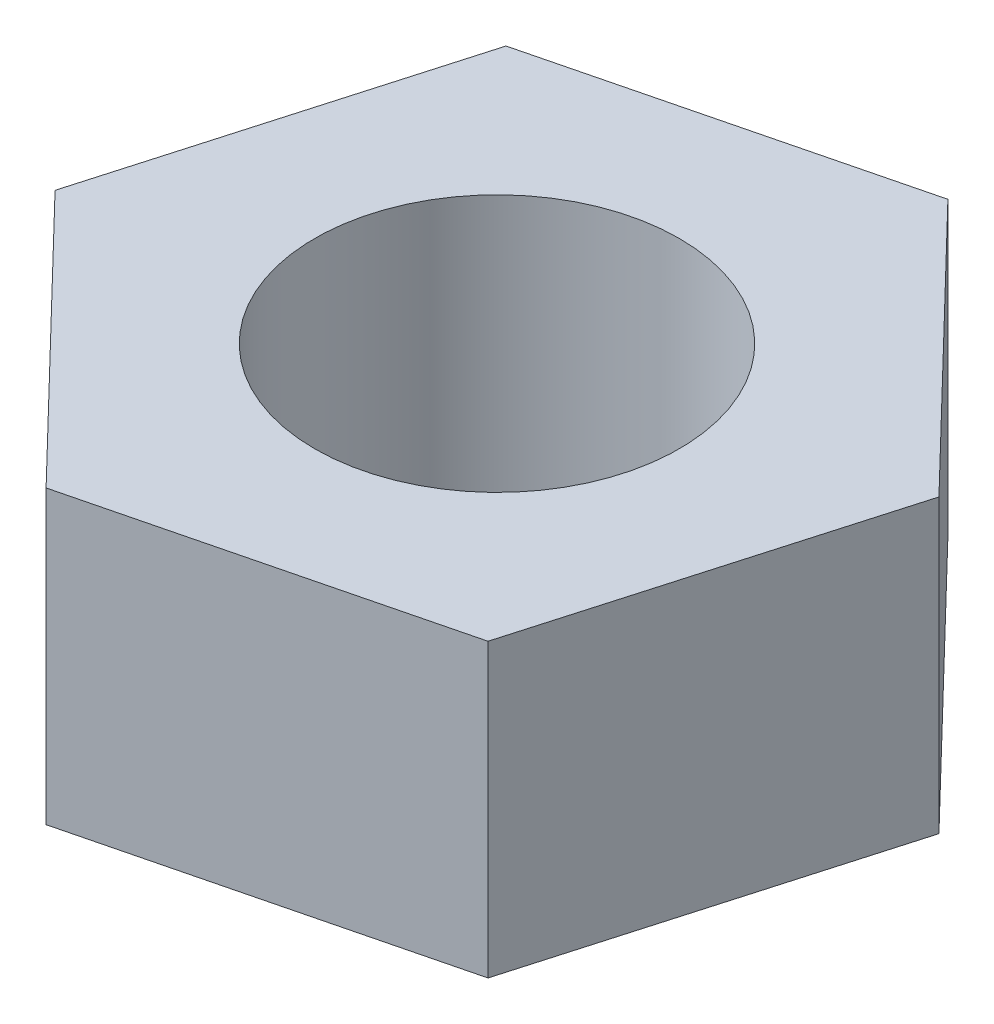
SolidWorks part; units mm, degrees
ref_plane "Front Plane" through (0, 0, 0) normal (0, 0, 1) x (1, 0, 0)
ref_plane "Top Plane" through (0, 0, 0) normal (0, 1, 0) x (1, 0, 0)
ref_plane "Right Plane" through (0, 0, 0) normal (1, 0, 0) x (0, 0, -1)
sketch "Sketch1" plane through (0, 0, 0) normal (0, 1, 0) x (1, 0, 0)
  line L1 (6.1613, 1.5365) -> (1.75, 6.1041)
  line L2 (1.75, 6.1041) -> (-4.4113, 4.5676)
  line L3 (-4.4113, 4.5676) -> (-6.1613, -1.5365)
  line L4 (-6.1613, -1.5365) -> (-1.75, -6.1041)
  line L5 (-1.75, -6.1041) -> (4.4113, -4.5676)
  line L6 (4.4113, -4.5676) -> (6.1613, 1.5365)
  circle A1 centre (0, 0) radius 3.175
  circle A2 centre (0, 0) radius 5.4993 construction
  dimension "D1" = 12.7
  dimension "D2" = 6.35
extrude "Boss-Extrude2" add sketch "Sketch1" along normal blind 5.08
